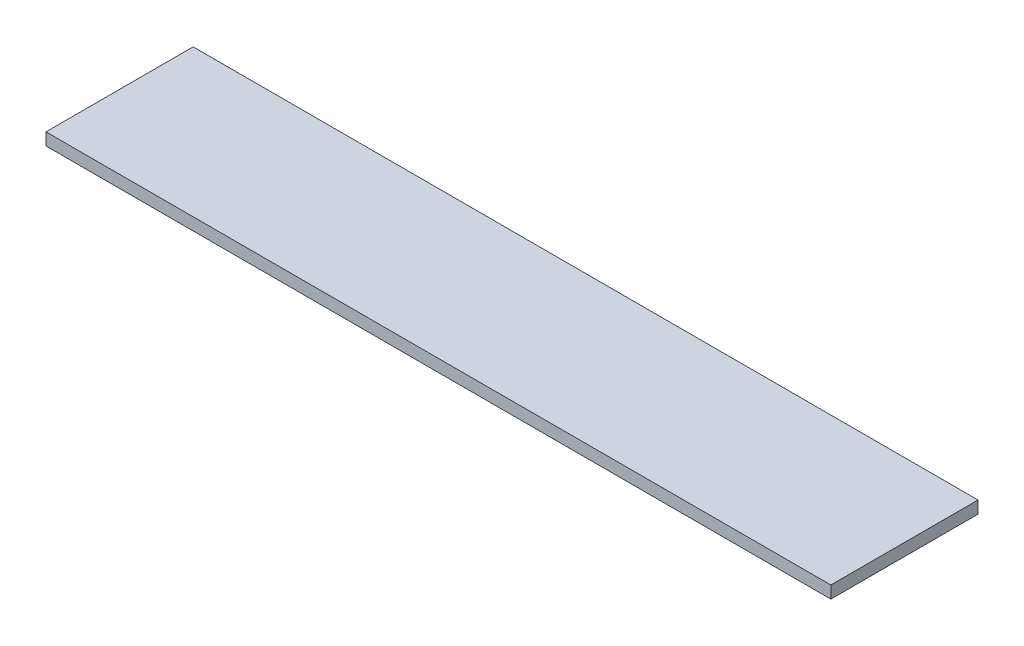
SolidWorks part; units mm, degrees
material "6061-T6 (SS)"
ref_plane "Front Plane" through (0, 0, 0) normal (0, 0, 1) x (1, 0, 0)
ref_plane "Top Plane" through (0, 0, 0) normal (0, 1, 0) x (1, 0, 0)
ref_plane "Right Plane" through (0, 0, 0) normal (1, 0, 0) x (0, 0, -1)
sketch "Sketch1" plane through (0, 0, 0) normal (0, 1, 0) x (1, 0, 0)
  line L1 (0, 0) -> (406.4, 0)
  line L2 (0, 0) -> (0, 76.2)
  line L3 (0, 76.2) -> (406.4, 76.2)
  line L4 (406.4, 0) -> (406.4, 76.2)
  dimension "D1" = 406.4
  dimension "D2" = 76.2
extrude "Boss-Extrude1" add sketch "Sketch1" along normal blind 6.35
